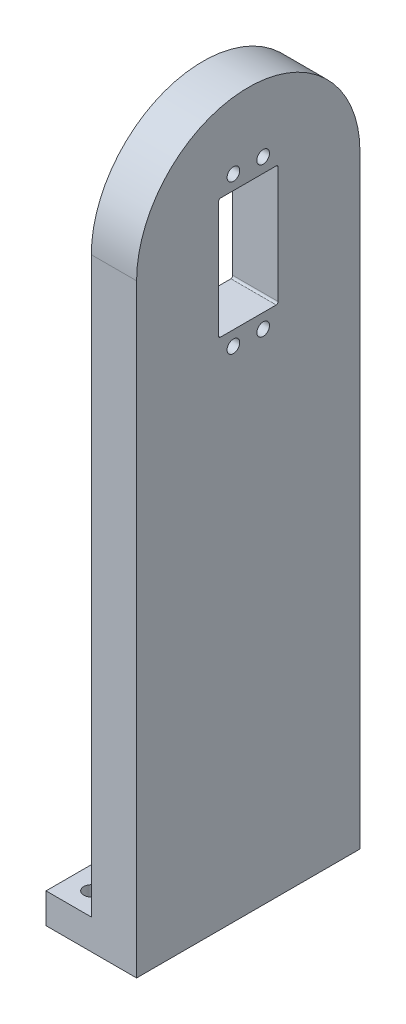
SolidWorks part; units mm, degrees
material "ABS"
ref_plane "Front Plane" through (0, 0, 0) normal (0, 0, 1) x (1, 0, 0)
ref_plane "Top Plane" through (0, 0, 0) normal (0, 1, 0) x (1, 0, 0)
ref_plane "Right Plane" through (0, 0, 0) normal (1, 0, 0) x (0, 0, -1)
sketch "Sketch1" plane through (0, 0, 0) normal (1, 0, 0) x (0, 0, -1)
  line L0 (-37, 0) -> (-37, -200)
  line L1 (-37, -200) -> (37, -200)
  line L2 (37, -200) -> (37, 0)
  arc A1 (37, 0) -> (-37, 0) centre (0, 0) ccw
  dimension "D3" = 200
extrude "Boss-Extrude1" add sketch "Sketch1" along normal blind 15
sketch "Sketch2" plane through (0, 0, 0) normal (-1, 0, 0) x (0, 0, 1)
  circle A0 centre (0, 0) radius 6.0045
sketch "Sketch3" plane through (15, 0, 0) normal (1, 0, 0) x (0, 0, -1)
  line L0 (9.8453, 9.2308) -> (9.85, -29.35)
  line L1 (9.2308, -30.0453) -> (-9.2308, -30.0453)
  line L2 (-9.8453, -29.4308) -> (-9.8453, 9.2308)
  line L3 (-9.2308, 9.8453) -> (9.2308, 9.8453)
  arc A0 (9.2308, 9.8453) -> (9.8453, 9.2308) centre (9.2308, 9.2308) cw
  arc A1 (9.85, -29.35) -> (9.2308, -30.0453) centre (9.1501, -29.3501) cw
  arc A4 (-9.2308, -30.0453) -> (-9.8453, -29.4308) centre (-9.2308, -29.4308) cw
  arc A5 (-9.8453, 9.2308) -> (-9.2308, 9.8453) centre (-9.2308, 9.2308) cw
extrude "Cut-Extrude2" cut sketch "Sketch3" against normal blind 15
sketch "Sketch4" plane through (0, -200, 0) normal (0, -1, 0) x (1, 0, 0)
  line L0 (0, 37) -> (-15, 37)
  line L1 (-15, 37) -> (-15, -37)
  line L2 (-15, -37) -> (0, -37)
  line L3 (0, -37) -> (0, 37)
  dimension "D1" = 15
extrude "Boss-Extrude2" add sketch "Sketch4" against normal blind 10
sketch "Sketch5" plane through (0, -190, 0) normal (0, 1, 0) x (1, 0, 0)
  line L0 (-15, -37) -> (-15, 37) construction
  line L1 (-15, 37) -> (0, 37) construction
  line L2 (0, -37) -> (-15, -37) construction
  circle A0 centre (-7.5, 29.5) radius 2.5
  circle A1 centre (-7.5, -29.5) radius 2.5
  dimension "D1" = 5
  dimension "D2" = 5
  dimension "D3" = 7.5
  dimension "D4" = 7.5
  dimension "D5" = 7.5
  dimension "D6" = 7.5
extrude "Cut-Extrude3" cut sketch "Sketch5" against normal blind 10
sketch "Sketch6" plane through (0, 0, 0) normal (-1, 0, 0) x (0, 0, 1)
  circle A0 centre (4.925, 14.6111) radius 2.1
  circle A1 centre (-4.925, 14.6111) radius 2.1
  circle A2 centre (4.925, -34.8111) radius 2.1
  circle A3 centre (-4.925, -34.8111) radius 2.1
extrude "Cut-Extrude4" cut sketch "Sketch6" against normal through all
